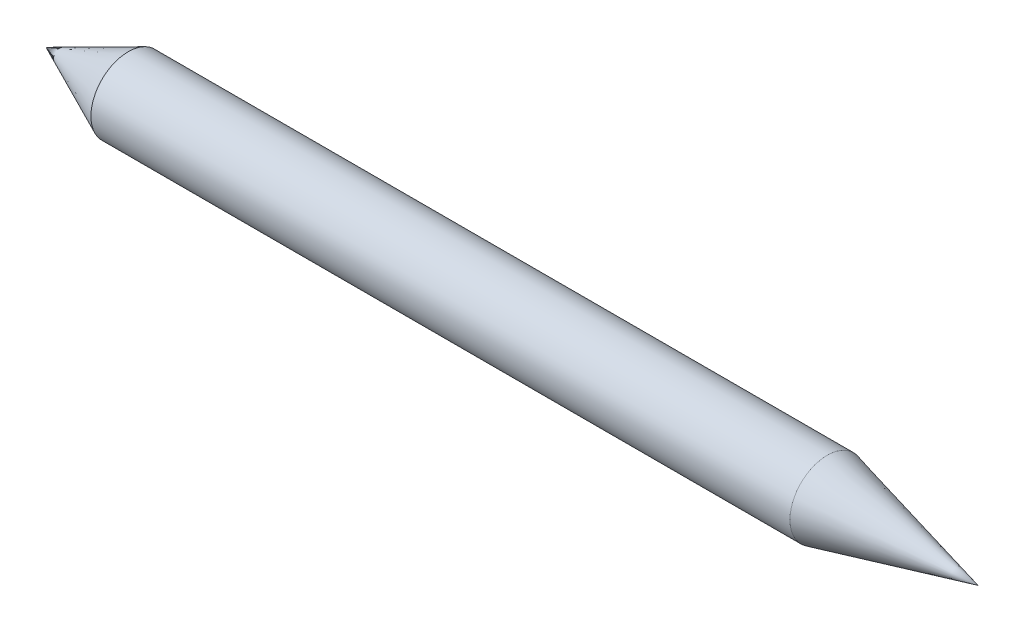
SolidWorks part; units mm, degrees
ref_plane "Alzado" through (0, 0, 0) normal (0, 0, 1) x (1, 0, 0)
ref_plane "Planta" through (0, 0, 0) normal (0, 1, 0) x (1, 0, 0)
ref_plane "Vista lateral" through (0, 0, 0) normal (1, 0, 0) x (0, 0, -1)
sketch "Croquis1" plane through (0, 0, 0) normal (0, 0, 1) x (1, 0, 0)
  line L0 (-79.0532, 7.1848) -> (120.9468, 7.1848)
  line L1 (120.9468, 7.1848) -> (88.5907, 15.1848)
  line L2 (88.5907, 15.1848) -> (-61.4093, 15.1848)
  line L3 (-61.4093, 15.1848) -> (-79.0532, 7.1848)
  dimension "D1" = 150
  dimension "D2" = 200
  dimension "D3" = 8
revolve "Revolución2" add sketch "Croquis1" angle 360 about L0
